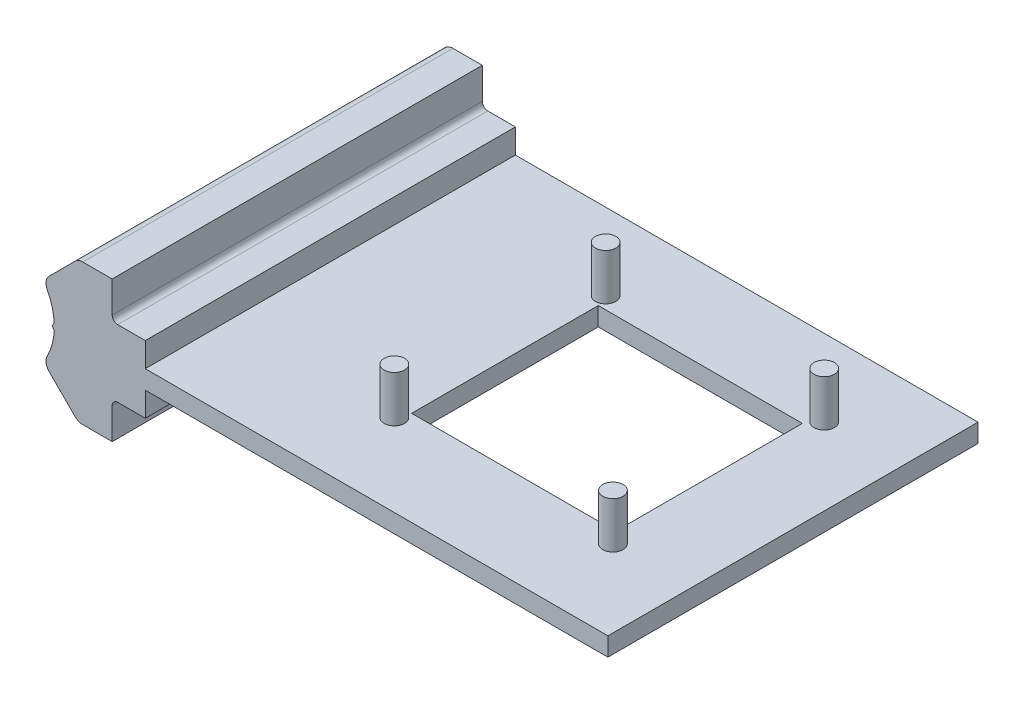
SolidWorks part; units mm, degrees
ref_plane "Front Plane" through (0, 0, 0) normal (0, 0, 1) x (1, 0, 0)
ref_plane "Top Plane" through (0, 0, 0) normal (0, 1, 0) x (1, 0, 0)
ref_plane "Right Plane" through (0, 0, 0) normal (1, 0, 0) x (0, 0, -1)
sketch "Sketch1" plane through (0, 0, 438.3589) normal (0, 0, 1) x (1, 0, 0)
  line L311 (42.5097, 19.3043) -> (42.5097, 15.9553)
  line L312 (42.5097, 15.9553) -> (106.0097, 15.9553)
  line L313 (106.0097, 15.9553) -> (106.0097, 13.4153)
  line L314 (106.0097, 13.4153) -> (42.5097, 13.4153)
  line L315 (42.5097, 13.4153) -> (42.5097, 10.0663)
  line L321 (38.7252, 10.0663) -> (42.5097, 10.0663)
  line L322 (37.9672, 5.0163) -> (37.9672, 9.3083)
  line L323 (33.929, 5.0163) -> (37.9672, 5.0163)
  line L324 (29.3226, 8.9998) -> (32.8655, 5.4569)
  line L325 (29.7071, 14.6853) -> (30.0175, 14.242)
  line L326 (30.0175, 15.1286) -> (29.7071, 14.6853)
  line L327 (32.8655, 23.9138) -> (29.3226, 20.3709)
  line L328 (42.5097, 19.3043) -> (38.7252, 19.3043)
  line L329 (37.9672, 24.3543) -> (33.929, 24.3543)
  line L330 (37.9672, 20.0623) -> (37.9672, 24.3543)
  line L331 (38.7252, 10.0663) -> (42.5097, 10.0663)
  line L332 (37.9672, 5.0163) -> (37.9672, 9.3083)
  line L333 (33.929, 5.0163) -> (37.9672, 5.0163)
  line L334 (29.3226, 8.9998) -> (32.8655, 5.4569)
  line L335 (29.7071, 14.6853) -> (30.0175, 14.242)
  line L336 (30.0175, 15.1286) -> (29.7071, 14.6853)
  line L337 (32.8655, 23.9138) -> (29.3226, 20.3709)
  line L338 (42.5097, 19.3043) -> (38.7252, 19.3043)
  line L339 (37.9672, 24.3543) -> (33.929, 24.3543)
  line L340 (37.9672, 20.0623) -> (37.9672, 24.3543)
  arc A323 (38.7252, 10.0663) -> (37.9672, 9.3083) centre (38.7252, 9.3083) ccw
  arc A324 (32.8655, 5.4569) -> (33.929, 5.0163) centre (33.929, 6.5203) ccw
  arc A325 (29.0566, 10.7665) -> (29.3226, 8.9998) centre (30.386, 10.0633) ccw
  arc A326 (29.0566, 10.7665) -> (30.0175, 14.242) centre (21.6482, 14.6853) ccw
  arc A327 (30.0175, 15.1286) -> (29.0566, 18.6041) centre (21.6482, 14.6853) ccw
  arc A328 (29.3226, 20.3709) -> (29.0566, 18.6041) centre (30.386, 19.3074) ccw
  arc A329 (33.929, 24.3543) -> (32.8655, 23.9138) centre (33.929, 22.8503) ccw
  arc A330 (37.9672, 20.0623) -> (38.7252, 19.3043) centre (38.7252, 20.0623) ccw
  arc A331 (38.7252, 10.0663) -> (37.9672, 9.3083) centre (38.7252, 9.3083) ccw
  arc A332 (32.8655, 5.4569) -> (33.929, 5.0163) centre (33.929, 6.5203) ccw
  arc A333 (29.0566, 10.7665) -> (29.3226, 8.9998) centre (30.386, 10.0633) ccw
  arc A334 (29.0566, 10.7665) -> (30.0175, 14.242) centre (21.6482, 14.6853) ccw
  arc A335 (30.0175, 15.1286) -> (29.0566, 18.6041) centre (21.6482, 14.6853) ccw
  arc A336 (29.3226, 20.3709) -> (29.0566, 18.6041) centre (30.386, 19.3074) ccw
  arc A337 (33.929, 24.3543) -> (32.8655, 23.9138) centre (33.929, 22.8503) ccw
  arc A338 (37.9672, 20.0623) -> (38.7252, 19.3043) centre (38.7252, 20.0623) ccw
  dimension "D2" = 2.54
  dimension "D3" = 63.5
  dimension "D1" = 0.381
extrude "Boss-Extrude1" add sketch "Sketch1" against normal blind 50.8
sketch "Sketch3" plane through (0, 15.9553, 0) normal (0, 1, 0) x (1, 0, 0)
  circle A0 centre (65.4119, -398.0724) radius 1.397
  circle A1 centre (95.4119, -398.0724) radius 1.397
  circle A2 centre (95.4119, -427.0724) radius 1.397
  circle A3 centre (65.4119, -427.0724) radius 1.397
  dimension "D1" = 2.794
extrude "Boss-Extrude2" add sketch "Sketch3" along normal blind 6.35
sketch "Sketch4" plane through (0, 15.9553, 0) normal (0, 1, 0) x (1, 0, 0)
  line L0 (62.9119, -395.5724) -> (97.9119, -395.5724) construction
  line L1 (66.0869, -399.7634) -> (94.1019, -399.7634)
  line L2 (66.0869, -399.7634) -> (66.0869, -425.3814)
  line L3 (66.0869, -425.3814) -> (94.1019, -425.3814)
  line L4 (94.1019, -399.7634) -> (94.1019, -425.3814)
  line L5 (97.9119, -429.5724) -> (62.9119, -429.5724) construction
  line L6 (97.9119, -395.5724) -> (97.9119, -429.5724) construction
  line L7 (62.9119, -429.5724) -> (62.9119, -395.5724) construction
  dimension "D1" = 4.191
  dimension "D2" = 4.191
  dimension "D3" = 3.81
  dimension "D4" = 3.175
extrude "Cut-Extrude1" cut sketch "Sketch4" against normal through all
